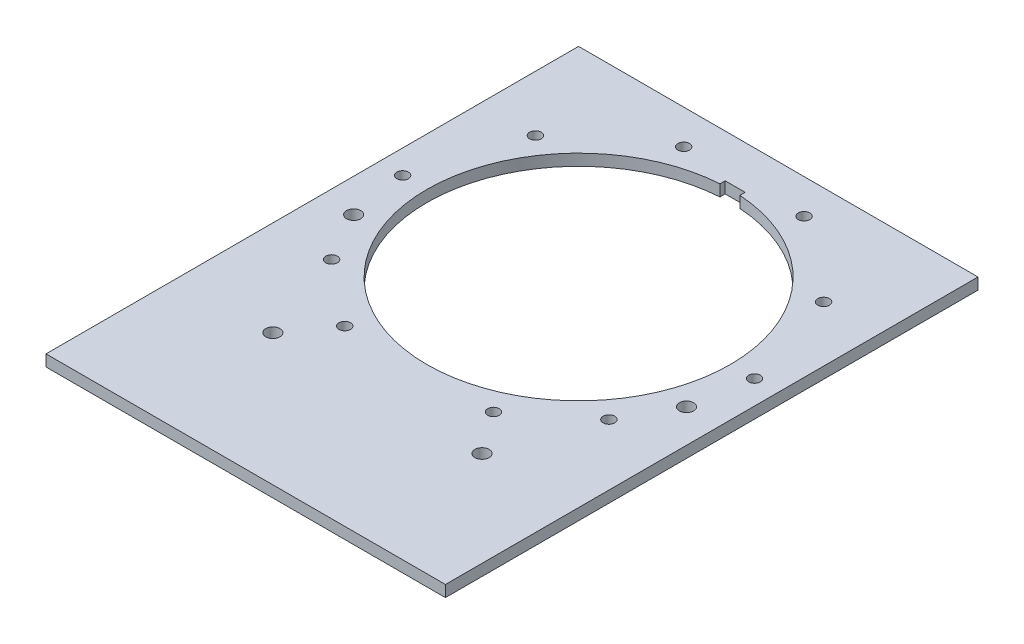
SolidWorks part; units mm, degrees
ref_plane "Plan de face" through (0, 0, 0) normal (0, 0, 1) x (1, 0, 0)
ref_plane "Plan de dessus" through (0, 0, 0) normal (0, 1, 0) x (1, 0, 0)
ref_plane "Plan de droite" through (0, 0, 0) normal (1, 0, 0) x (0, 0, -1)
sketch "Esquisse1" plane through (0, 0, 0) normal (0, 1, 0) x (1, 0, 0)
  line L2 (0, 0) -> (151.5431, 106.1116) construction
  line L3 (-210, 210) -> (210, 210)
  line L4 (-210, 210) -> (-210, -350)
  line L5 (0, 0) -> (-63.2737, 173.8431) construction
  line L8 (0, 210) -> (0, -210) construction
  line L10 (-529.9181, 0) -> (445.2416, 0) construction
  line L13 (0, 0) -> (63.2737, 173.8431) construction
  line L14 (10.5, 164.654) -> (10.5, 159.154)
  line L16 (-210, -350) -> (210, -350)
  line L17 (210, 210) -> (210, -350)
  line L22 (10.5, 164.654) -> (-10.5, 164.654)
  line L27 (0, 0) -> (-145.782, -113.8974) construction
  line L29 (0, 0) -> (-151.5431, 106.1116) construction
  line L31 (-10.5, 164.654) -> (-10.5, 159.154)
  line L34 (0, 0) -> (-78.1844, -167.6669) construction
  line L35 (0, 0) -> (145.782, -113.8974) construction
  line L36 (0, 0) -> (78.1844, -167.6669) construction
  arc A0 (-10.5, 159.154) -> (10.5, 159.154) centre (0, 0) ccw
  circle A2 centre (-63.2737, 173.8431) radius 6.1
  circle A3 centre (-175, -61.5) radius 7.5
  circle A4 centre (110.0032, -211.5) radius 7.5
  circle A5 centre (175, -61.5) radius 7.5
  circle A6 centre (0, 0) radius 185 construction
  circle A7 centre (185, 0) radius 6.1
  circle A8 centre (-109.9968, -211.5) radius 7.5
  circle A9 centre (151.5431, 106.1116) radius 6.1
  circle A10 centre (-151.5431, 106.1116) radius 6.1
  circle A11 centre (-185, 0) radius 6.1
  circle A12 centre (63.2737, 173.8431) radius 6.1
  circle A17 centre (-145.782, -113.8974) radius 6.1
  circle A18 centre (-78.1844, -167.6669) radius 6.1
  circle A19 centre (145.782, -113.8974) radius 6.1
  circle A20 centre (78.1844, -167.6669) radius 6.1
  point P11 (0, -350)
  point P32 (0, 0)
  point P50 (0, -80)
  point P51 (0, -191.5)
  point P58 (0, -230)
  point P60 (-210, 0)
  point P68 (0, 159.5)
  dimension "D2" = 319
  dimension "D3" = 420
  dimension "D4" = 35
  dimension "D5" = 220
  dimension "D6" = 350
  dimension "D7" = 35
  dimension "D11" = 35
  dimension "D12" = 35
  dimension "D13" = 210
  dimension "D14" = 150
  dimension "D8" = 370
  dimension "D10" = 38
  dimension "D15" = 12.2
  dimension "D17" = 21
  dimension "D21" = 15
  dimension "D23" = 350
  dimension "D9" = 61.5
  dimension "D16" = 175
  dimension "D18" = 5.5
  dimension "D19" = 27
other "AlignerGroupe1"
extrude "Boss.-Extru.1" add sketch "Esquisse1" along normal blind 12
sketch "Esquisse2" plane through (0, 12, 0) normal (0, 1, 0) x (1, 0, 0)
  line L0 (210, -191.5) -> (-210, -191.5)
  line L1 (210, -350) -> (210, 210) construction
  line L2 (-210, 210) -> (-210, -350) construction
  line L3 (210, -41.5) -> (154.0065, -41.5)
  line L4 (-154.0065, -41.5) -> (-210, -41.5)
  arc A0 (-10.5, 159.154) -> (10.5, 159.154) centre (0, 0) ccw construction
  circle A1 centre (175, -61.5) radius 7.5 construction
  circle A2 centre (110.0032, -211.5) radius 7.5 construction
  dimension "D1" = 20
  dimension "D2" = 20
extrude "GRAVAGE" [suppressed] cut sketch "Esquisse2" against normal blind 0.5 thin
